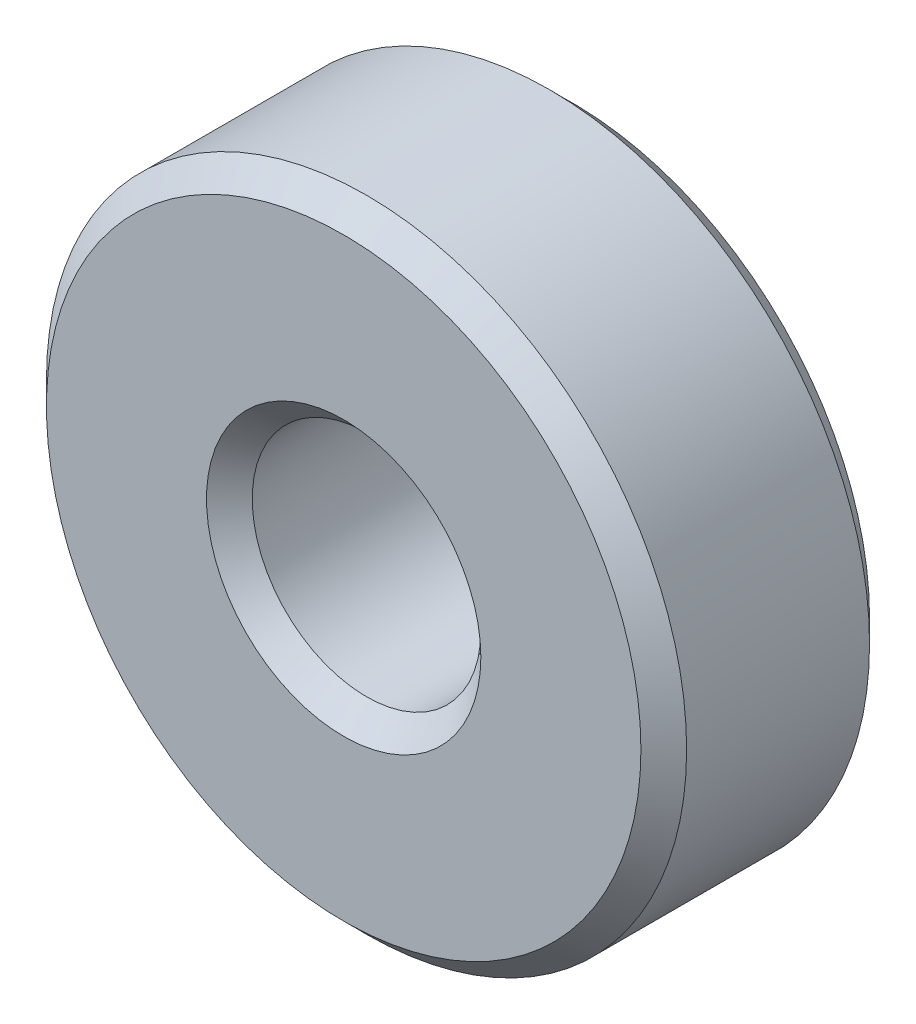
SolidWorks part; units mm, degrees
material "Plain Carbon Steel"
ref_plane "Front Plane" through (0, 0, 0) normal (0, 0, 1) x (1, 0, 0)
ref_plane "Top Plane" through (0, 0, 0) normal (0, 1, 0) x (1, 0, 0)
ref_plane "Right Plane" through (0, 0, 0) normal (1, 0, 0) x (0, 0, -1)
sketch "Sketch1" plane through (0, 0, 0) normal (0, 0, 1) x (1, 0, 0)
  circle A0 centre (0, 0) radius 2.5
  circle A1 centre (0, 0) radius 7
  dimension "D1" = 5
  dimension "D2" = 14
extrude "Boss-Extrude1" add sketch "Sketch1" along normal blind 5
chamfer "Chamfer1" distance 0.5 angle 45 4 edges at (2.5, 0, 0) (7, 0, 0) (2.5, 0, 5) (7, 0, 5)
